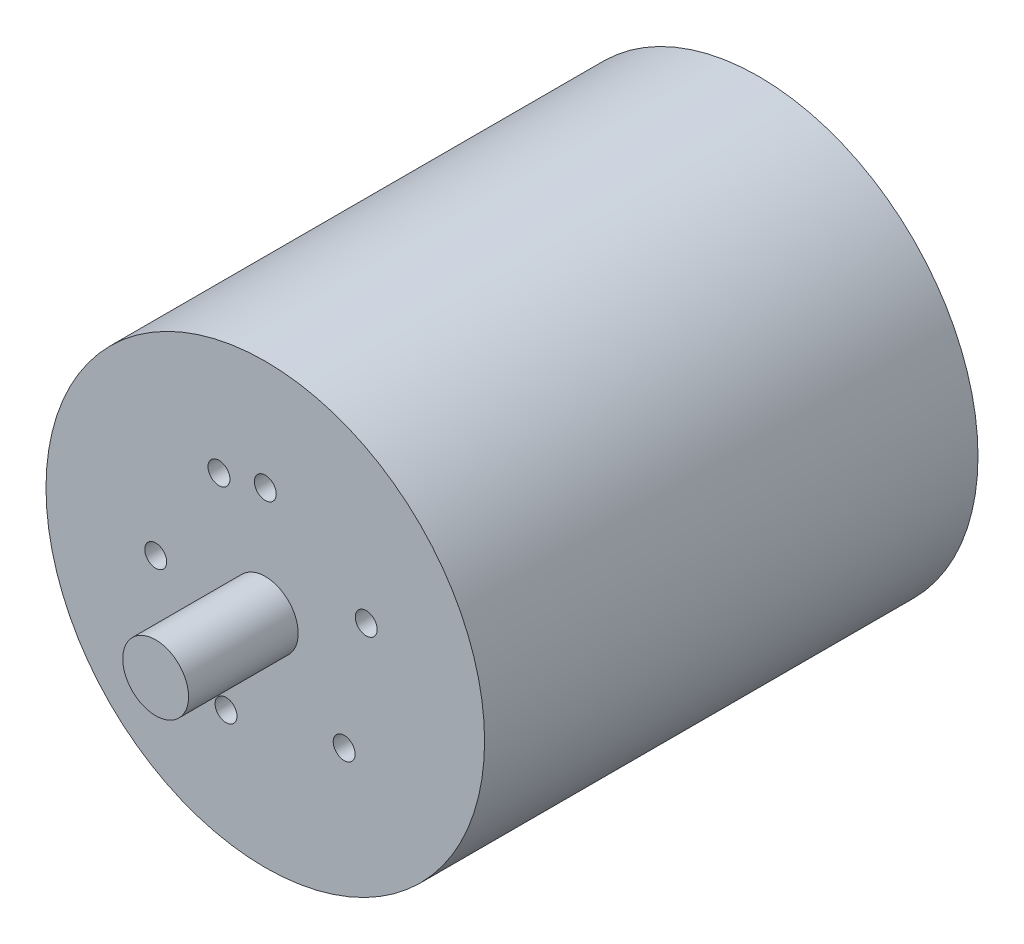
SolidWorks part; units mm, degrees
ref_plane "Front Plane" through (0, 0, 0) normal (0, 0, 1) x (1, 0, 0)
ref_plane "Top Plane" through (0, 0, 0) normal (0, 1, 0) x (1, 0, 0)
ref_plane "Right Plane" through (0, 0, 0) normal (1, 0, 0) x (0, 0, -1)
sketch "Sketch1" plane through (0, 0, 0) normal (0, 0, 1) x (1, 0, 0)
  circle A0 centre (0, 0) radius 20
  dimension "D1" = 40
extrude "Boss-Extrude1" add sketch "Sketch1" along normal mid plane 45
sketch "Sketch2" plane through (0, 0, 22.5) normal (0, 0, 1) x (1, 0, 0)
  circle A0 centre (0, 0) radius 3
  dimension "D1" = 6
extrude "Boss-Extrude2" add sketch "Sketch2" along normal blind 10
sketch "Sketch3" plane through (0, 0, 22.5) normal (0, 0, 1) x (1, 0, 0)
  circle A0 centre (0, 10) radius 1
  dimension "D1" = 2
  dimension "D2" = 10
extrude "Cut-Extrude1" cut sketch "Sketch3" against normal blind 2
pattern_circular "CirPattern1" count 6 every 67 about axis through (0, 0, 0) along (0, 0, 1) of "Cut-Extrude1"
